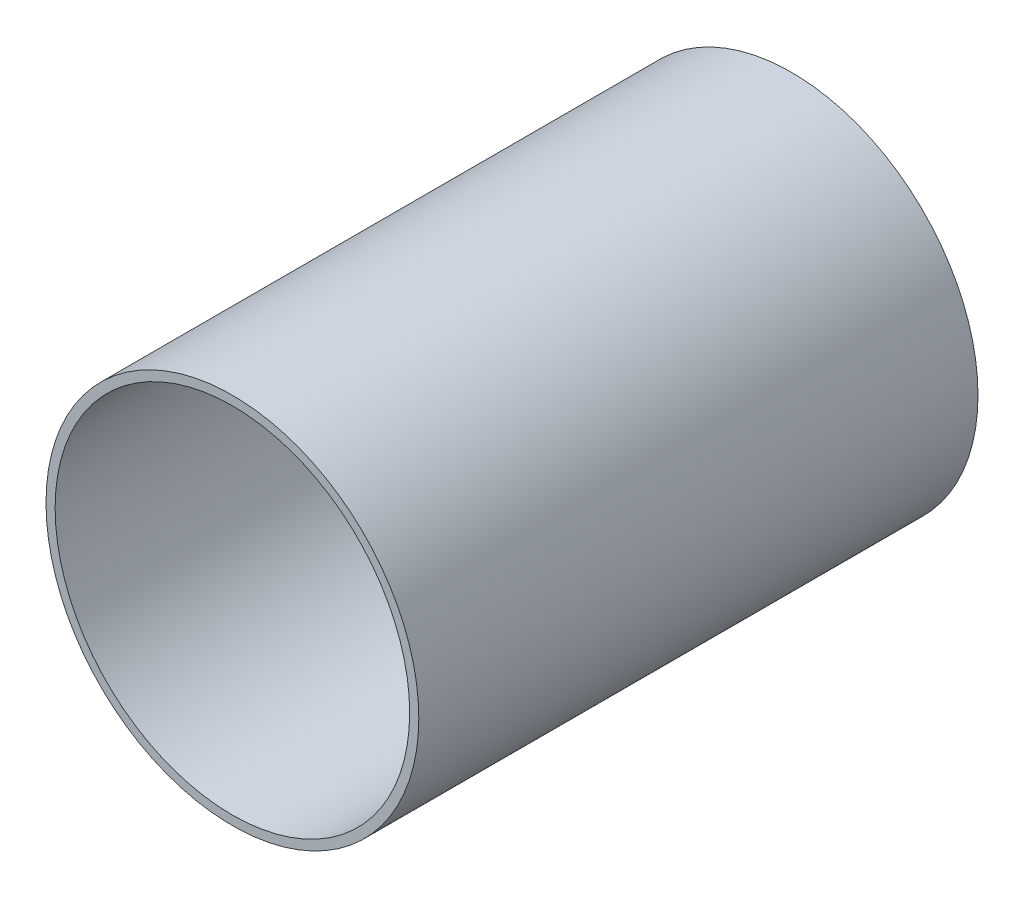
SolidWorks part; units mm, degrees
material "Plain Carbon Steel"
ref_plane "Front Plane" through (0, 0, 0) normal (0, 0, 1) x (1, 0, 0)
ref_plane "Top Plane" through (0, 0, 0) normal (0, 1, 0) x (1, 0, 0)
ref_plane "Right Plane" through (0, 0, 0) normal (1, 0, 0) x (0, 0, -1)
sketch "Sketch2" plane through (0, 0, 0) normal (0, 0, 1) x (1, 0, 0)
  circle A0 centre (0, 0) radius 25.4
  circle A1 centre (0, 0) radius 24.1554
  dimension "D1" = 1.2446
extrude "Boss-Extrude1" add sketch "Sketch2" along normal blind 76.2
